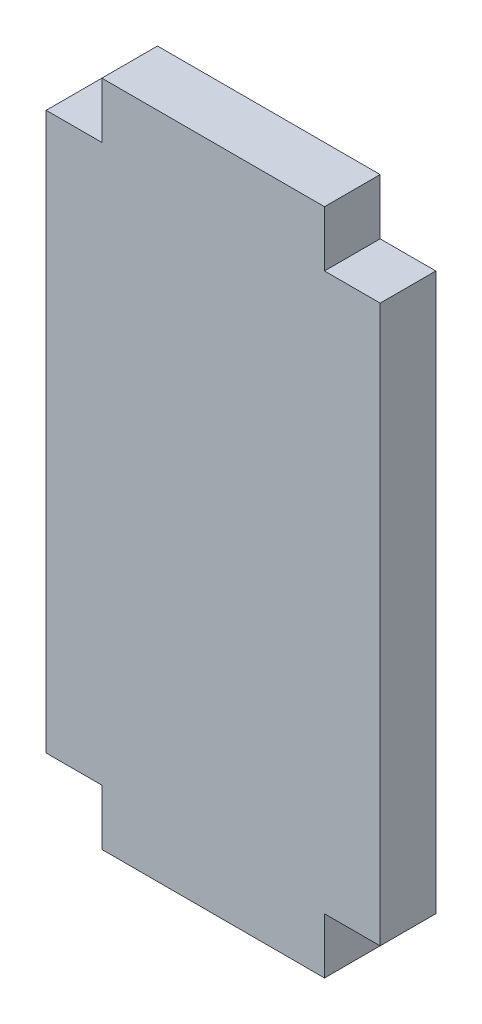
SolidWorks part; units mm, degrees
ref_plane "Plan de face" through (0, 0, 0) normal (0, 0, 1) x (1, 0, 0)
ref_plane "Plan de dessus" through (0, 0, 0) normal (0, 1, 0) x (1, 0, 0)
ref_plane "Plan de droite" through (0, 0, 0) normal (1, 0, 0) x (0, 0, -1)
sketch "Esquisse1" plane through (0, 0, 0) normal (0, 0, 1) x (1, 0, 0)
  line L0 (28.5988, 46.0417) -> (33.5988, 46.0417)
  line L1 (33.5988, 46.0417) -> (33.5988, 51.0417)
  line L2 (33.5988, 51.0417) -> (53.5988, 51.0417)
  line L3 (53.5988, 51.0417) -> (53.5988, 46.0417)
  line L4 (53.5988, 46.0417) -> (58.5988, 46.0417)
  line L5 (58.5988, 46.0417) -> (58.5988, -3.9583)
  line L6 (58.5988, -3.9583) -> (53.5988, -3.9583)
  line L7 (53.5988, -3.9583) -> (53.5988, -8.9583)
  line L8 (53.5988, -8.9583) -> (33.5988, -8.9583)
  line L9 (33.5988, -8.9583) -> (33.5988, -3.9583)
  line L10 (33.5988, -3.9583) -> (28.5988, -3.9583)
  line L11 (28.5988, -3.9583) -> (28.5988, 46.0417)
  dimension "D1" = 5
  dimension "D2" = 5
  dimension "D3" = 50
  dimension "D4" = 30
  dimension "D5" = 20
  dimension "D6" = 5
  dimension "D7" = 20
  dimension "D8" = 5
extrude "Boss.-Extru.1" add sketch "Esquisse1" along normal blind 5
